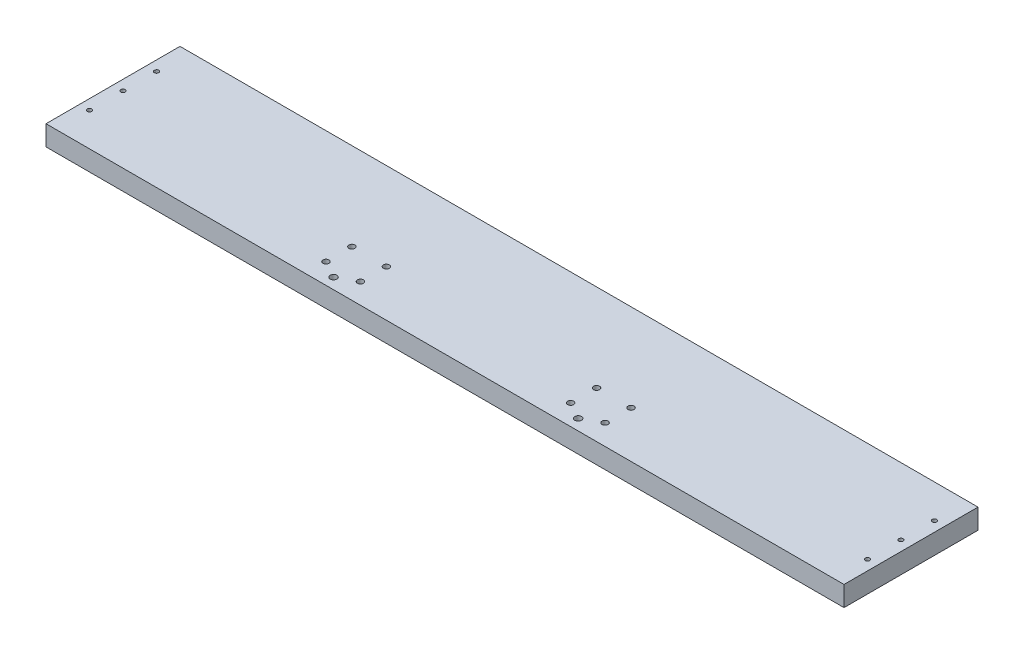
SolidWorks part; units mm, degrees
ref_plane "Front Plane" through (0, 0, 0) normal (0, 0, 1) x (1, 0, 0)
ref_plane "Top Plane" through (0, 0, 0) normal (0, 1, 0) x (1, 0, 0)
ref_plane "Right Plane" through (0, 0, 0) normal (1, 0, 0) x (0, 0, -1)
sketch "Sketch2" plane through (0, 0, 0) normal (0, 1, 0) x (1, 0, 0)
  line L1 (0, 0) -> (756.412, 0)
  line L2 (0, 0) -> (0, 127)
  line L3 (0, 127) -> (756.412, 127)
  line L4 (756.412, 0) -> (756.412, 127)
  dimension "D1" = 127
  dimension "D2" = 756.412
extrude "Boss-Extrude1" add sketch "Sketch2" along normal blind 19.05
sketch "Sketch3" plane through (0, 19.05, 0) normal (0, 1, 0) x (1, 0, 0)
  circle A0 centre (245.9291, 19.4628) radius 2.8511
  circle A1 centre (278.5808, 19.4628) radius 2.8511
  circle A2 centre (278.5808, 44.0373) radius 2.8511
  circle A3 centre (245.9291, 44.0373) radius 2.8511
  circle A4 centre (477.8311, 19.4628) radius 2.8511
  circle A5 centre (510.4828, 19.4628) radius 2.8511
  circle A6 centre (510.4828, 44.0373) radius 2.8511
  circle A7 centre (477.8311, 44.0373) radius 2.8511
extrude "Cut-Extrude1" cut sketch "Sketch3" against normal up to next
sketch "Sketch4" plane through (0, 19.05, 0) normal (0, 1, 0) x (1, 0, 0)
  line L0 (262.255, 12.7) -> (262.255, 10.3188) construction
  line L2 (494.157, 12.7) -> (494.157, 10.3188) construction
  circle A0 centre (494.157, 10.3188) radius 3.175
  circle A1 centre (262.255, 10.3188) radius 3.175
  dimension "D1" = 6.35
  dimension "D3" = 6.35
  dimension "D2" = 2.3813
  dimension "D4" = 2.3813
extrude "Cut-Extrude2" cut sketch "Sketch4" against normal up to next
sketch "Sketch5" plane through (0, 19.05, 0) normal (0, 1, 0) x (1, 0, 0)
  line L0 (9.525, 127) -> (9.525, 95.25) construction
  line L1 (756.412, 127) -> (0, 127) construction
  line L2 (9.525, 95.25) -> (9.525, 31.75) construction
  line L3 (9.525, 31.75) -> (9.525, 0) construction
  line L4 (0, 0) -> (756.412, 0) construction
  line L5 (0, 127) -> (0, 0) construction
  line L6 (378.206, 127) -> (378.206, 0) construction
  line L7 (746.887, 31.75) -> (746.887, 0) construction
  line L8 (746.887, 95.25) -> (746.887, 31.75) construction
  line L9 (746.887, 127) -> (746.887, 95.25) construction
  circle A0 centre (9.525, 95.25) radius 2.0828
  circle A1 centre (9.525, 63.5) radius 2.0828
  circle A2 centre (9.525, 31.75) radius 2.0828
  circle A3 centre (746.887, 31.75) radius 2.0828
  circle A4 centre (746.887, 63.5) radius 2.0828
  circle A5 centre (746.887, 95.25) radius 2.0828
  dimension "D2" = 4.1656
  dimension "D1" = 63.5
  dimension "D3" = 9.525
extrude "Cut-Extrude3" cut sketch "Sketch5" against normal up to next
